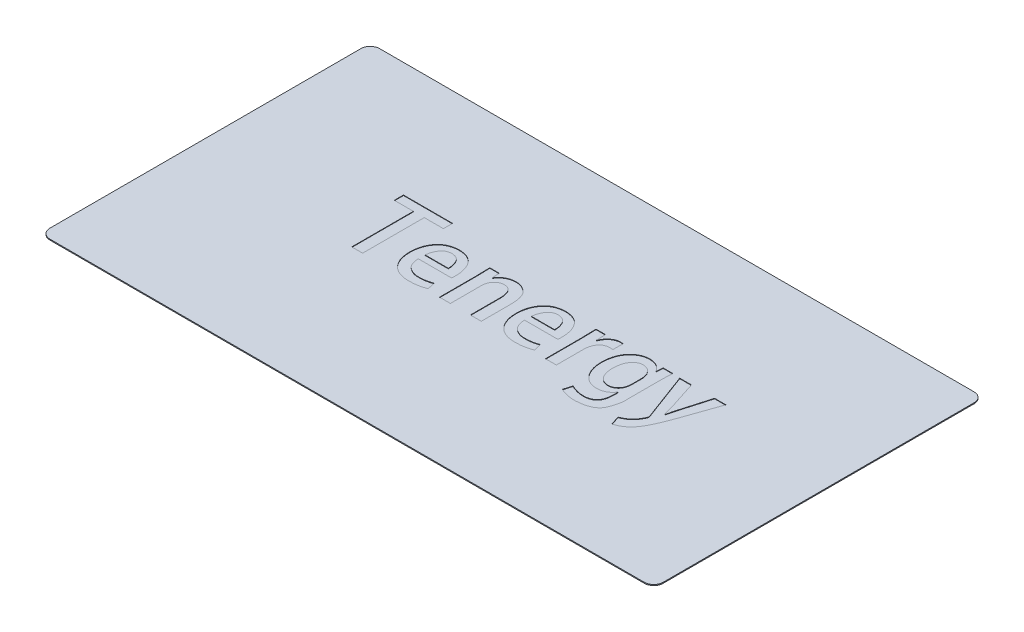
SolidWorks part; units mm, degrees
ref_plane "Front Plane" through (0, 0, 0) normal (0, 0, 1) x (1, 0, 0)
ref_plane "Top Plane" through (0, 0, 0) normal (0, 1, 0) x (1, 0, 0)
ref_plane "Right Plane" through (0, 0, 0) normal (1, 0, 0) x (0, 0, -1)
sketch "Sketch1" plane through (0, 0, 0) normal (0, 1, 0) x (1, 0, 0)
  line L1 (-64.9, 34.9) -> (64.9, 34.9)
  line L2 (-64.9, 34.9) -> (-64.9, -34.9)
  line L3 (-64.9, -34.9) -> (64.9, -34.9)
  line L4 (64.9, 34.9) -> (64.9, -34.9)
  line L5 (-64.9, 34.9) -> (64.9, -34.9) construction
  line L6 (-64.9, -34.9) -> (64.9, 34.9) construction
  point P0 (0, 0)
  dimension "D1" = 129.8
  dimension "D2" = 69.8
extrude "Boss-Extrude1" add sketch "Sketch1" along normal blind 0.2
fillet "Fillet1" radius 2 4 edges at (-64.9, 0.1, -34.9) (64.9, 0.1, -34.9) (64.9, 0.1, 34.9) (-64.9, 0.1, 34.9)
sketch "Sketch2" plane through (0, 0.2, 0) normal (0, 1, 0) x (1, 0, 0)
  text T0 "Tenergy "
extrude "Cut-Extrude1" [suppressed] cut sketch "Sketch2" against normal blind 0.1
sketch "Sketch3" plane through (0, 0.2, 0) normal (0, 1, 0) x (1, 0, 0)
  text T0 "Tenergy" font "@Adobe 黑体 Std R" height 15
extrude "Cut-Extrude4" cut sketch "Sketch3" against normal blind 0.1
